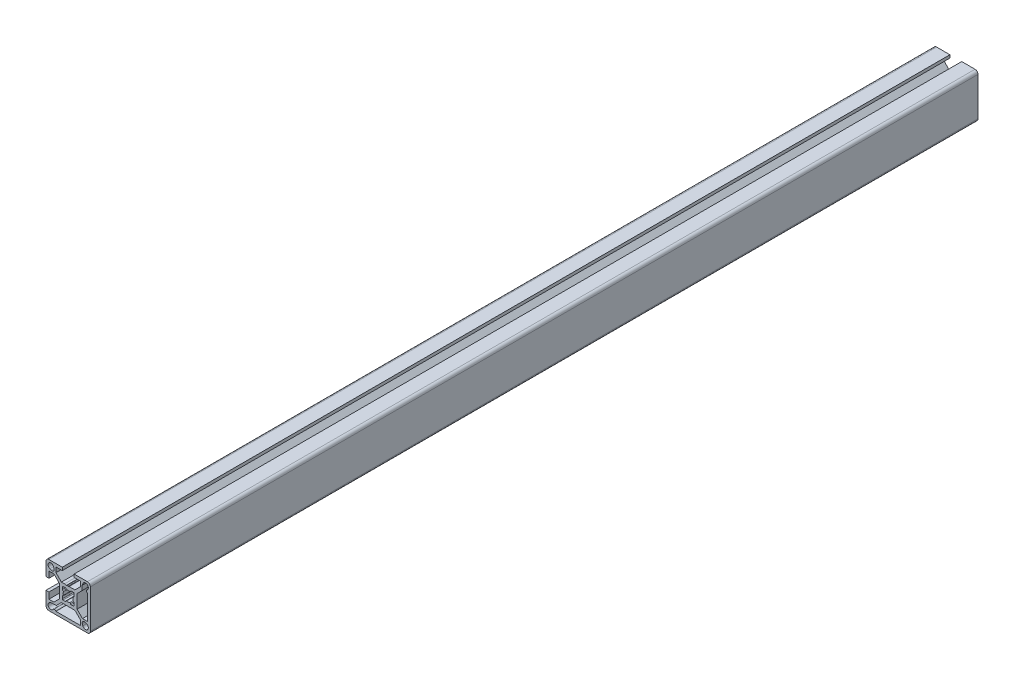
SolidWorks part; units mm, degrees
material "6063-T5"
ref_plane "Piano frontale" through (0, 0, 0) normal (0, 0, 1) x (1, 0, 0)
ref_plane "Piano superiore" through (0, 0, 0) normal (0, 1, 0) x (1, 0, 0)
ref_plane "Piano destro" through (0, 0, 0) normal (1, 0, 0) x (0, 0, -1)
ref_plane "Piano1" through (0, 0, -600) normal (0, 0, -1) x (-1, 0, 0)
sketch "Schizzo1" plane through (0, 0, -600) normal (0, 0, -1) x (-1, 0, 0)
  line L0 (12.3498, 9.9146) -> (11.3422, 9.5479)
  line L1 (9.5479, 11.3422) -> (9.9146, 12.3498)
  line L2 (-4.5858, -6) -> (4.58, -6)
  line L3 (8.03, -9.45) -> (11.1, -9.45)
  line L4 (11.1, -9.45) -> (12.3619, -9.919)
  line L5 (8.3553, -13) -> (-8.25, -13)
  line L6 (-8.25, -13) -> (-8.25, -9.6642)
  line L7 (-9.919, 12.3619) -> (-9.45, 11.1)
  line L8 (-9.45, 11.1) -> (-9.45, 8.03)
  line L9 (-6, 4.58) -> (-6, -4.5858)
  line L10 (-9.6642, -8.25) -> (-13, -8.25)
  line L11 (-13, -8.25) -> (-13, 8.3553)
  line L12 (-9.5479, -11.3422) -> (-9.9146, -12.3498)
  line L13 (-12.3498, -9.9146) -> (-11.3422, -9.5479)
  line L14 (4, 3.5) -> (4, 2)
  line L15 (4, -2) -> (4, -3.5)
  line L16 (3.5, -4) -> (2, -4)
  line L17 (-2, -4) -> (-3.5, -4)
  line L18 (-4, -3.5) -> (-4, -2)
  line L19 (-4, 2) -> (-4, 3.5)
  line L20 (-3.5, 4) -> (-2, 4)
  line L21 (2, 4) -> (3.5, 4)
  line L22 (-15, 13) -> (-15, -13)
  line L23 (-13, -15) -> (13, -15)
  line L24 (15, -13) -> (15, -4)
  line L25 (15, -4) -> (13, -4)
  line L26 (13, -4) -> (13, -8.25)
  line L27 (13, -8.25) -> (9.6642, -8.25)
  line L28 (6, -4.5858) -> (6, -2.5)
  line L29 (6, -2.5) -> (5.751, -1.2189)
  line L30 (5.751, -1.2189) -> (5.933, -0.9036)
  line L31 (5.933, -0.4036) -> (5.7, 0)
  line L32 (5.7, 0) -> (5.933, 0.4036)
  line L33 (6, 0.6536) -> (6, 4.5858)
  line L34 (9.6642, 8.25) -> (13, 8.25)
  line L35 (13, 8.25) -> (13, 4)
  line L36 (13, 4) -> (15, 4)
  line L37 (15, 4) -> (15, 13)
  line L38 (13, 15) -> (4, 15)
  line L39 (4, 15) -> (4, 13)
  line L40 (4, 13) -> (8.25, 13)
  line L41 (8.25, 13) -> (8.25, 9.6642)
  line L42 (4.5858, 6) -> (2.5, 6)
  line L43 (2.5, 6) -> (1.2189, 5.751)
  line L44 (1.2189, 5.751) -> (0.9036, 5.933)
  line L45 (0.4036, 5.933) -> (0, 5.7)
  line L46 (0, 5.7) -> (-0.4036, 5.933)
  line L47 (-0.6536, 6) -> (-4.5858, 6)
  line L48 (-8.25, 9.6642) -> (-8.25, 13)
  line L49 (-8.25, 13) -> (-4, 13)
  line L50 (-4, 13) -> (-4, 15)
  line L51 (-4, 15) -> (-13, 15)
  arc A0 (9.9146, 12.3498) -> (12.3498, 9.9146) centre (11.7, 11.7) cw
  arc A1 (11.3422, 9.5479) -> (9.5479, 11.3422) centre (10.8634, 10.8634) cw
  arc A2 (12.3619, -9.919) -> (10.1276, -12.7665) centre (11.7, -11.7) cw
  arc A3 (10.1276, -12.7665) -> (8.3553, -13) centre (9.3, -13.3279) ccw
  arc A4 (-13, 8.3553) -> (-12.7665, 10.1276) centre (-13.3279, 9.3) ccw
  arc A5 (-12.7665, 10.1276) -> (-9.919, 12.3619) centre (-11.7, 11.7) cw
  arc A6 (-9.9146, -12.3498) -> (-12.3498, -9.9146) centre (-11.7, -11.7) cw
  arc A7 (-11.3422, -9.5479) -> (-9.5479, -11.3422) centre (-10.8634, -10.8634) cw
  arc A8 (4, 2) -> (3.5746, 1.5056) centre (3.5, 2) cw
  arc A9 (3.5746, 1.5056) -> (3.2517, 0.9932) centre (3.6342, 1.1101) ccw
  arc A10 (3.2517, 0.9932) -> (3.2517, -0.9932) centre (0, 0) cw
  arc A11 (3.2517, -0.9932) -> (3.5746, -1.5056) centre (3.6342, -1.1101) ccw
  arc A12 (3.5746, -1.5056) -> (4, -2) centre (3.5, -2) cw
  arc A13 (4, -3.5) -> (3.5, -4) centre (3.5, -3.5) cw
  arc A14 (2, -4) -> (1.5056, -3.5746) centre (2, -3.5) cw
  arc A15 (1.5056, -3.5746) -> (0.9932, -3.2517) centre (1.1101, -3.6342) ccw
  arc A16 (0.9932, -3.2517) -> (-0.9932, -3.2517) centre (0, 0) cw
  arc A17 (-0.9932, -3.2517) -> (-1.5056, -3.5746) centre (-1.1101, -3.6342) ccw
  arc A18 (-1.5056, -3.5746) -> (-2, -4) centre (-2, -3.5) cw
  arc A19 (-3.5, -4) -> (-4, -3.5) centre (-3.5, -3.5) cw
  arc A20 (-4, -2) -> (-3.5746, -1.5056) centre (-3.5, -2) cw
  arc A21 (-3.5746, -1.5056) -> (-3.2517, -0.9932) centre (-3.6342, -1.1101) ccw
  arc A22 (-3.2517, -0.9932) -> (-3.2517, 0.9932) centre (0, 0) cw
  arc A23 (-3.2517, 0.9932) -> (-3.5746, 1.5056) centre (-3.6342, 1.1101) ccw
  arc A24 (-3.5746, 1.5056) -> (-4, 2) centre (-3.5, 2) cw
  arc A25 (-4, 3.5) -> (-3.5, 4) centre (-3.5, 3.5) cw
  arc A26 (-2, 4) -> (-1.5056, 3.5746) centre (-2, 3.5) cw
  arc A27 (-1.5056, 3.5746) -> (-0.9932, 3.2517) centre (-1.1101, 3.6342) ccw
  arc A28 (-0.9932, 3.2517) -> (0.9932, 3.2517) centre (0, 0) cw
  arc A29 (0.9932, 3.2517) -> (1.5056, 3.5746) centre (1.1101, 3.6342) ccw
  arc A30 (1.5056, 3.5746) -> (2, 4) centre (2, 3.5) cw
  arc A31 (3.5, 4) -> (4, 3.5) centre (3.5, 3.5) cw
  arc A32 (-15, -13) -> (-13, -15) centre (-13, -13) ccw
  arc A33 (13, -15) -> (15, -13) centre (13, -13) ccw
  arc A34 (5.933, -0.9036) -> (5.933, -0.4036) centre (5.5, -0.6536) ccw
  arc A35 (5.933, 0.4036) -> (6, 0.6536) centre (5.5, 0.6536) ccw
  arc A36 (15, 13) -> (13, 15) centre (13, 13) ccw
  arc A37 (0.9036, 5.933) -> (0.4036, 5.933) centre (0.6536, 5.5) ccw
  arc A38 (-0.4036, 5.933) -> (-0.6536, 6) centre (-0.6536, 5.5) ccw
  arc A39 (-13, 15) -> (-15, 13) centre (-13, 13) ccw
  spline S0 degree 3 poles (4.58, -6) (5.73, -7.15) (6.88, -8.3) (8.03, -9.45) knots 0 0 0 0 1 1 1 1
  spline S1 degree 3 poles (-8.25, -9.6642) (-7.0286, -8.4428) (-5.8072, -7.2214) (-4.5858, -6) knots 0 0 0 0 1 1 1 1
  spline S2 degree 3 poles (-9.45, 8.03) (-8.3, 6.88) (-7.15, 5.73) (-6, 4.58) knots 0 0 0 0 1 1 1 1
  spline S3 degree 3 poles (-6, -4.5858) (-7.2214, -5.8072) (-8.4428, -7.0286) (-9.6642, -8.25) knots 0 0 0 0 1 1 1 1
  spline S4 degree 3 poles (9.6642, -8.25) (8.4428, -7.0286) (7.2214, -5.8072) (6, -4.5858) knots 0 0 0 0 1 1 1 1
  spline S5 degree 3 poles (6, 4.5858) (7.2214, 5.8072) (8.4428, 7.0286) (9.6642, 8.25) knots 0 0 0 0 1 1 1 1
  spline S6 degree 3 poles (8.25, 9.6642) (7.0286, 8.4428) (5.8072, 7.2214) (4.5858, 6) knots 0 0 0 0 1 1 1 1
  spline S7 degree 3 poles (-4.5858, 6) (-5.8072, 7.2214) (-7.0286, 8.4428) (-8.25, 9.6642) knots 0 0 0 0 1 1 1 1
extrude "Estrusione-Estrusione1" add sketch "Schizzo1" against normal blind 600
